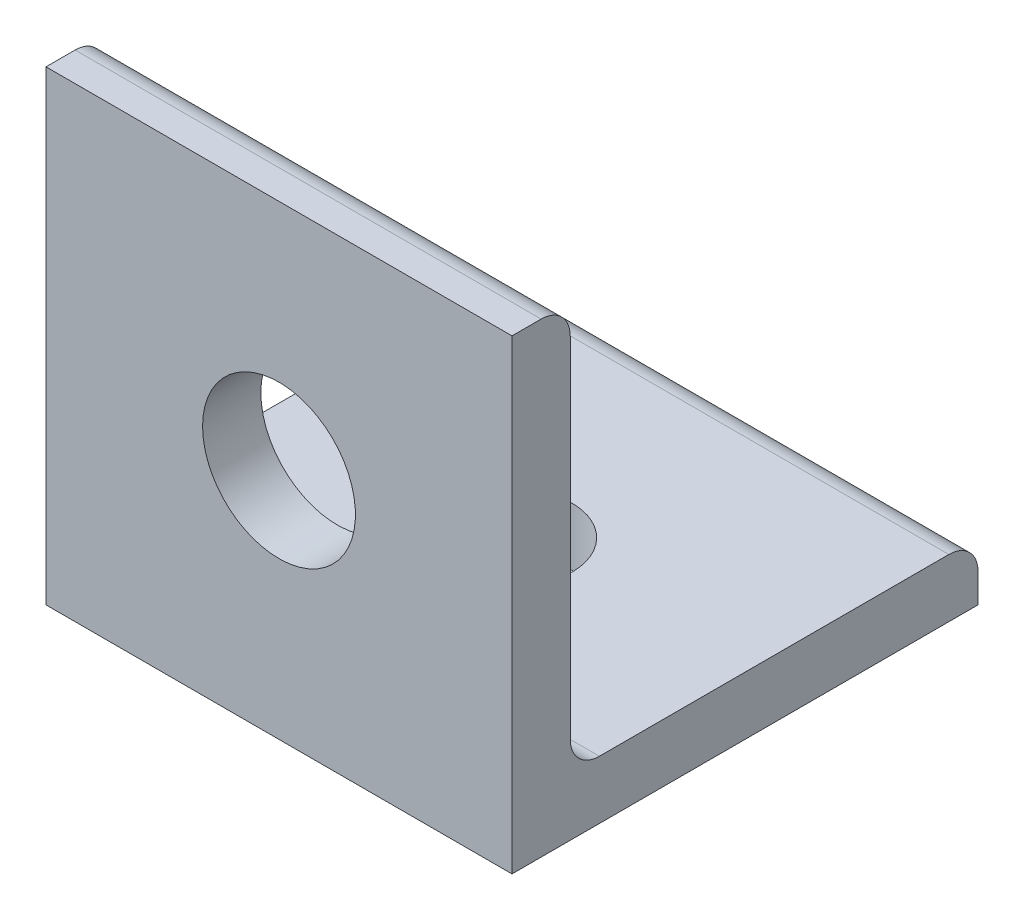
SolidWorks part; units mm, degrees
material "6061-T6 (SS)"
ref_plane "Front Plane" through (0, 0, 0) normal (0, 0, 1) x (1, 0, 0)
ref_plane "Top Plane" through (0, 0, 0) normal (0, 1, 0) x (1, 0, 0)
ref_plane "Right Plane" through (0, 0, 0) normal (1, 0, 0) x (0, 0, -1)
sketch "Sketch1" plane through (0, 0, 0) normal (1, 0, 0) x (0, 0, -1)
  line L0 (0, 0) -> (0, 25.4)
  line L1 (0, 0) -> (25.4, 0)
  dimension "D1" = 25.4
extrude "Extrude-Thin1" add sketch "Sketch1" along normal mid plane 25.4 thin
sketch "Sketch2" plane through (0, 0, -3.175) normal (0, 0, -1) x (-1, 0, 0)
  line L0 (0, 25.4) -> (0, 12.7) construction
  line L1 (-12.7, 25.4) -> (12.7, 25.4) construction
  circle A0 centre (0, 12.7) radius 4.1656
  dimension "D2" = 8.3312
  dimension "D1" = 12.7
extrude "Cut-Extrude1" cut sketch "Sketch2" against normal through all
sketch "Sketch3" plane through (0, 3.175, 0) normal (0, 1, 0) x (1, 0, 0)
  line L0 (0, 25.4) -> (0, 12.7) construction
  line L1 (12.7, 25.4) -> (-12.7, 25.4) construction
  circle A0 centre (0, 12.7) radius 3.2639
  dimension "D2" = 6.5278
  dimension "D1" = 12.7
extrude "Cut-Extrude2" cut sketch "Sketch3" against normal through all
fillet "Fillet1" radius 1.5875 3 edges at (0, 3.175, -25.4) (0, 3.175, -3.175) (0, 25.4, -3.175)
